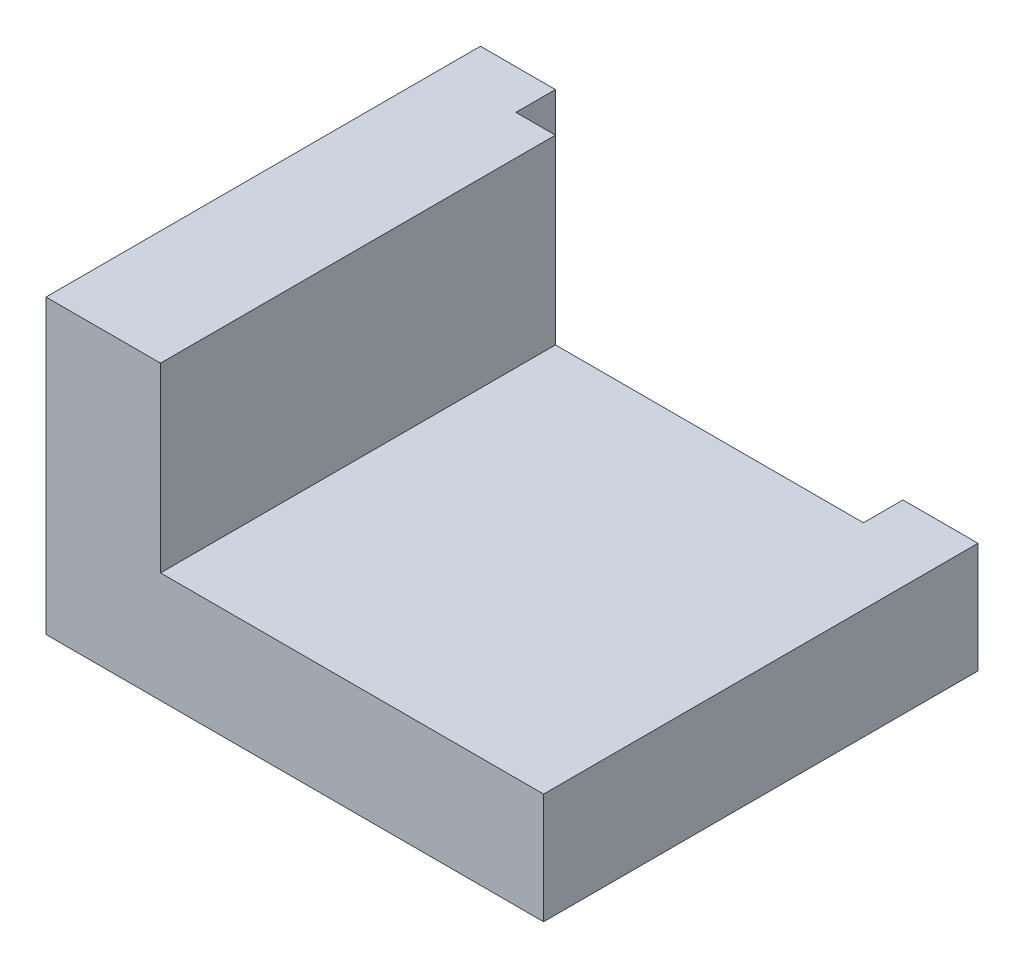
SolidWorks part; units mm, degrees
ref_plane "Front Plane" through (0, 0, 0) normal (0, 0, 1) x (1, 0, 0)
ref_plane "Top Plane" through (0, 0, 0) normal (0, 1, 0) x (1, 0, 0)
ref_plane "Right Plane" through (0, 0, 0) normal (1, 0, 0) x (0, 0, -1)
sketch "Sketch1" plane through (0, 0, 0) normal (0, 0, 1) x (1, 0, 0)
  line L0 (0, 0) -> (0, 37)
  line L1 (0, 37) -> (9.5, 37)
  line L2 (9.5, 37) -> (9.5, 4)
  line L3 (9.5, 4) -> (53.5, 4)
  line L4 (53.5, 4) -> (53.5, 14)
  line L5 (53.5, 14) -> (63, 14)
  line L6 (63, 14) -> (63, 0)
  line L7 (63, 0) -> (0, 0)
  dimension "D1" = 9.5
  dimension "D2" = 9.5
  dimension "D3" = 14
  dimension "D4" = 63
  dimension "D5" = 4
  dimension "D6" = 37
extrude "Boss-Extrude1" add sketch "Sketch1" along normal blind 5
sketch "Sketch2" plane through (0, 0, 5) normal (0, 0, 1) x (1, 0, 0)
  line L0 (0, 37) -> (14.5, 37)
  line L1 (14.5, 37) -> (14.5, 14)
  line L2 (14.5, 14) -> (63, 14)
  line L3 (63, 0) -> (63, 14) construction
  line L4 (63, 14) -> (63, 0)
  line L5 (63, 0) -> (0, 0)
  line L6 (0, 0) -> (0, 37)
  dimension "D1" = 14.5
  dimension "D2" = 14
extrude "Boss-Extrude3" add sketch "Sketch2" along normal blind 50
